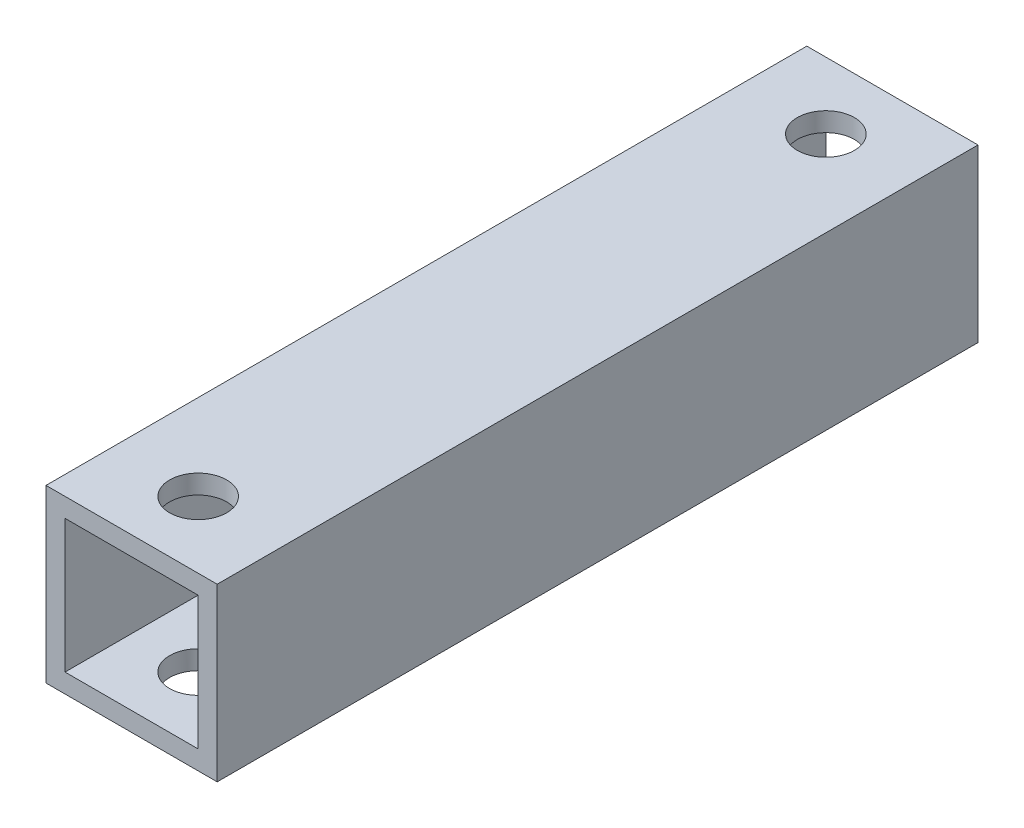
SolidWorks part; units mm, degrees
ref_plane "正面" through (0, 0, 0) normal (0, 0, 1) x (1, 0, 0)
ref_plane "平面" through (0, 0, 0) normal (0, 1, 0) x (1, 0, 0)
ref_plane "右側面" through (0, 0, 0) normal (1, 0, 0) x (0, 0, -1)
sketch "ｽｹｯﾁ1" plane through (0, 0, 0) normal (0, 0, 1) x (1, 0, 0)
  line L1 (-4.5, 4.5) -> (4.5, 4.5)
  line L2 (-4.5, 4.5) -> (-4.5, -4.5)
  line L3 (-4.5, -4.5) -> (4.5, -4.5)
  line L4 (4.5, 4.5) -> (4.5, -4.5)
  line L5 (-4.5, 4.5) -> (4.5, -4.5) construction
  line L6 (-4.5, -4.5) -> (4.5, 4.5) construction
  point P0 (0, 0)
  dimension "D1" = 9
  dimension "D2" = 9
extrude "ﾎﾞｽ - 押し出し1" add sketch "ｽｹｯﾁ1" along normal blind 40
sketch "ｽｹｯﾁ2" plane through (0, 0, 40) normal (0, 0, 1) x (1, 0, 0)
  line L1 (-3.5, 3.5) -> (3.5, 3.5)
  line L2 (-3.5, 3.5) -> (-3.5, -3.5)
  line L3 (-3.5, -3.5) -> (3.5, -3.5)
  line L4 (3.5, 3.5) -> (3.5, -3.5)
  line L5 (-3.5, 3.5) -> (3.5, -3.5) construction
  line L6 (-3.5, -3.5) -> (3.5, 3.5) construction
  point P0 (0, 0)
  dimension "D1" = 7
  dimension "D2" = 7
extrude "ｶｯﾄ - 押し出し1" cut sketch "ｽｹｯﾁ2" against normal blind 40
sketch "ｽｹｯﾁ3" plane through (0, 4.5, 0) normal (0, 1, 0) x (1, 0, 0)
  line L0 (0, 0) -> (0, -3.5)
  line L1 (0, -40) -> (0, -36.5)
  line L2 (4.5, -40) -> (-4.5, -40) construction
  circle A0 centre (0, -3.5) radius 1.5
  circle A1 centre (0, -36.5) radius 1.5
  dimension "D2" = 3
  dimension "D4" = 3
  dimension "D1" = 3.5
  dimension "D3" = 3.5
extrude "ｶｯﾄ - 押し出し2" cut sketch "ｽｹｯﾁ3" against normal blind 38
